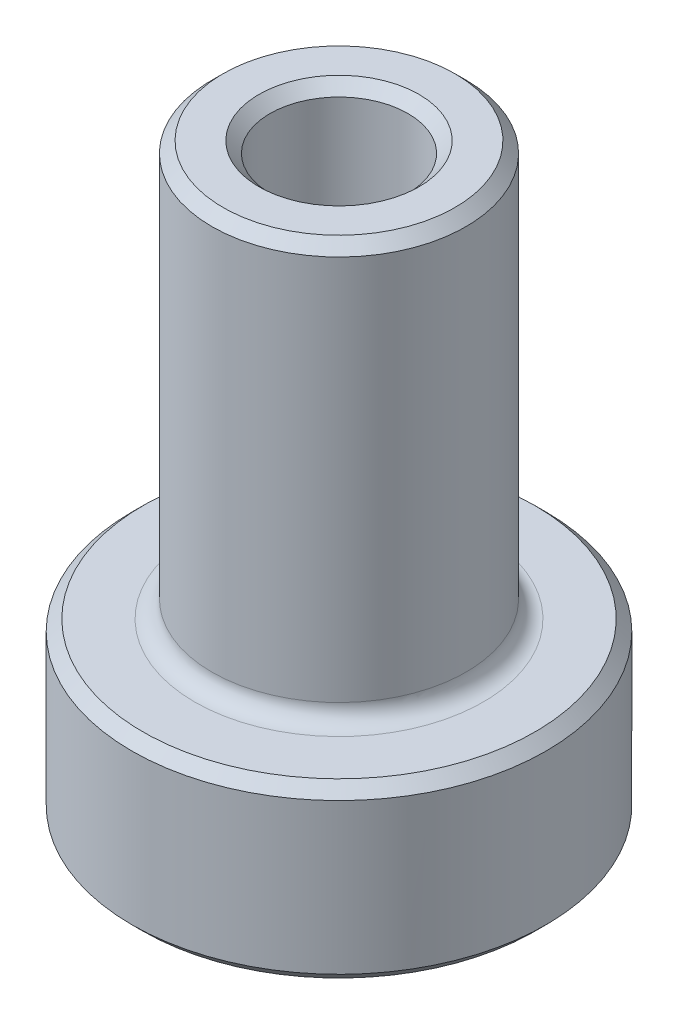
SolidWorks part; units mm, degrees
material "Onyx"
ref_plane "Front" through (0, 0, 0) normal (0, 0, 1) x (1, 0, 0)
ref_plane "Top" through (0, 0, 0) normal (0, 1, 0) x (1, 0, 0)
ref_plane "Right" through (0, 0, 0) normal (1, 0, 0) x (0, 0, -1)
sketch "Sketch1" plane through (0, 0, 0) normal (0, 0, 1) x (1, 0, 0)
  line L0 (0, 7.8865) -> (0, -7.8865) construction
  line L1 (1.5875, 0) -> (4.7625, 0)
  line L2 (4.7625, 0) -> (4.7625, 3.9688)
  line L3 (4.7625, 3.9688) -> (2.921, 3.9688)
  line L4 (2.921, 3.9688) -> (2.921, 13.4938)
  line L5 (2.921, 13.4938) -> (1.5875, 13.4938)
  line L6 (1.5875, 13.4938) -> (1.5875, 0)
  dimension "D1" = 3.9688
  dimension "D2" = 3.175
  dimension "D3" = 5.842
  dimension "D4" = 9.525
  dimension "D5" = 9.525
revolve "Revolve1" add sketch "Sketch1" angle 360 about L0
sketch "Sketch2" plane through (0, 0, 0) normal (0, -1, 0) x (1, 0, 0)
  line L1 (1.7598, 3.048) -> (-1.7598, 3.048)
  line L2 (-1.7598, 3.048) -> (-3.5195, 0)
  line L3 (-3.5195, 0) -> (-1.7598, -3.048)
  line L4 (-1.7598, -3.048) -> (1.7598, -3.048)
  line L5 (1.7598, -3.048) -> (3.5195, 0)
  line L6 (3.5195, 0) -> (1.7598, 3.048)
  circle A0 centre (0, 0) radius 3.048 construction
  dimension "D1" = 6.096
extrude "Cut-Extrude1" cut sketch "Sketch2" against normal blind 2.3813
fillet "Fillet1" radius 0.3969 1 edges at (0, 3.9688, 2.921)
fillet "Fillet2" radius 0.7937 12 edges at (2.6396, 2.3813, -1.524) (0, 2.3813, -3.048) (-2.6396, 2.3813, -1.524) (-2.6396, 2.3813, 1.524) (2.6396, 2.3813, 1.524) (0, 2.3813, 3.048) (3.5195, 1.1906, 0) (1.7598, 1.1906, -3.048) (-1.7598, 1.1906, -3.048) (-3.5195, 1.1906, 0) (1.7598, 1.1906, 3.048) (-1.7598, 1.1906, 3.048)
chamfer "Chamfer1" distance 0.254 angle 45 17 edges at (0, 0, 4.7625) (0, 3.9688, 4.7625) (0, 13.4938, 1.5875) (0, 13.4938, 2.921) (0, 2.3812, -1.5875) (0, 0, -3.048) (1.6984, 0, -2.9417) (-1.6984, 0, -2.9417) (2.6396, 0, -1.524) (-2.6396, 0, -1.524) (3.3967, 0, 0) (-3.3967, 0, 0) (2.6396, 0, 1.524) (-2.6396, 0, 1.524) (1.6984, 0, 2.9417) (-1.6984, 0, 2.9417) (0, 0, 3.048)
